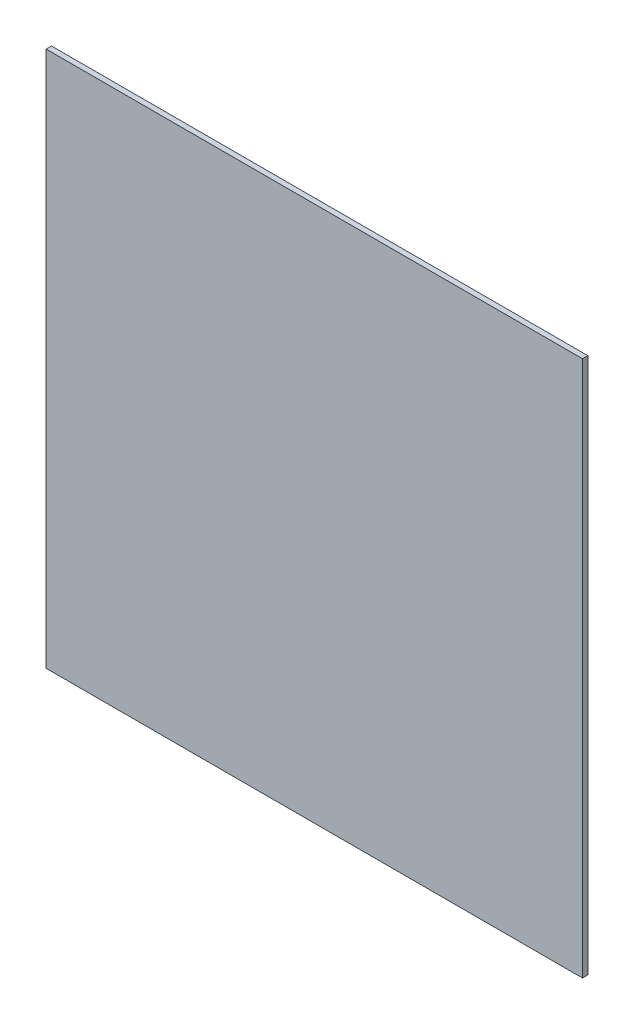
SolidWorks part; units mm, degrees
ref_plane "Plan de face" through (0, 0, 0) normal (0, 0, 1) x (1, 0, 0)
ref_plane "Plan de dessus" through (0, 0, 0) normal (0, 1, 0) x (1, 0, 0)
ref_plane "Plan de droite" through (0, 0, 0) normal (1, 0, 0) x (0, 0, -1)
sketch "Esquisse1" plane through (0, 0, 0) normal (0, 0, 1) x (1, 0, 0)
  line L1 (-70.0242, 98.3438) -> (229.9758, 98.3438)
  line L2 (-70.0242, 98.3438) -> (-70.0242, -201.6562)
  line L3 (-70.0242, -201.6562) -> (229.9758, -201.6562)
  line L4 (229.9758, 98.3438) -> (229.9758, -201.6562)
  point P4 (-201.6295, 17.4113)
  dimension "D1" = 300
extrude "Boss.-Extru.1" add sketch "Esquisse1" along normal blind 3
